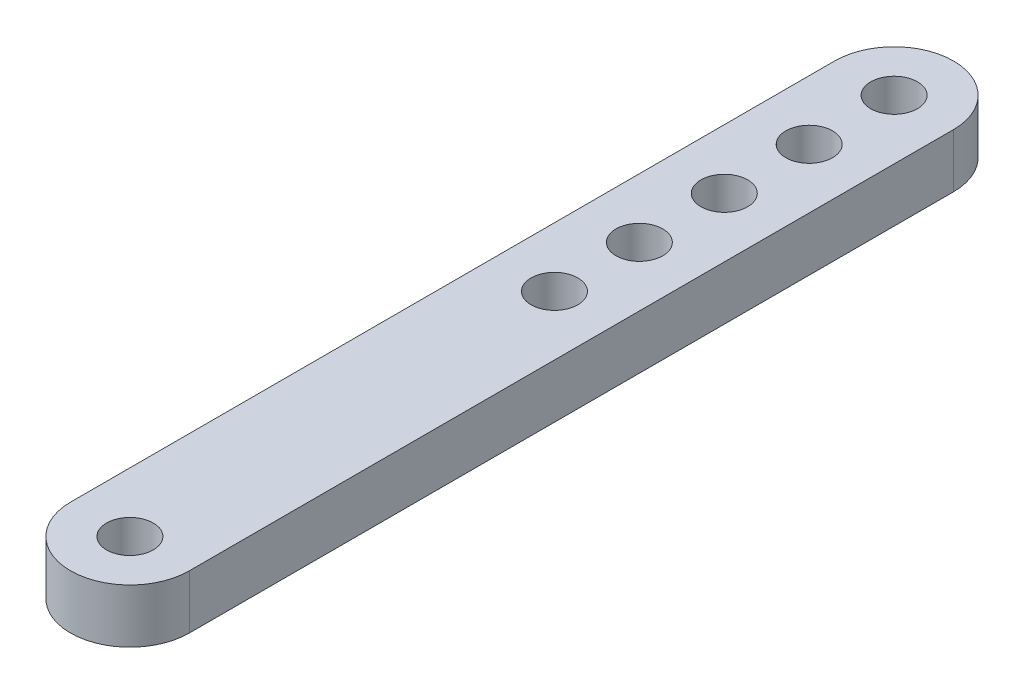
SolidWorks part; units mm, degrees
ref_plane "Front Plane" through (0, 0, 0) normal (0, 0, 1) x (1, 0, 0)
ref_plane "Top Plane" through (0, 0, 0) normal (0, 1, 0) x (1, 0, 0)
ref_plane "Right Plane" through (0, 0, 0) normal (1, 0, 0) x (0, 0, -1)
sketch "Sketch1" plane through (0, 0, 0) normal (0, 1, 0) x (1, 0, 0)
  line L0 (0, 90) -> (0, 0) construction
  line L1 (7, 90) -> (7, 0)
  line L2 (-7, 90) -> (-7, 0)
  arc A0 (7, 90) -> (-7, 90) centre (0, 90) ccw
  arc A1 (-7, 0) -> (7, 0) centre (0, 0) ccw
  circle A2 centre (0, 90) radius 2.75
  circle A3 centre (0, 0) radius 2.75
  point P2 (0, 45)
  point P11 (0, 0)
  dimension "D1" = 7
  dimension "D2" = 5.5
  dimension "D3" = 5.5
  dimension "D4" = 90
extrude "Boss-Extrude1" add sketch "Sketch1" along normal blind 6.35
sketch "Sketch2" plane through (0, 0, 0) normal (0, 1, 0) x (1, 0, 0)
  circle A0 centre (0, 90) radius 2.75
  circle A1 centre (0, 80) radius 2.75
  circle A2 centre (0, 70) radius 2.75
  circle A3 centre (0, 60) radius 2.75
  circle A4 centre (0, 50) radius 2.75
  dimension "D1" = 10
  dimension "D2" = 10
  dimension "D3" = 10
  dimension "D4" = 10
extrude "Cut-Extrude1" cut sketch "Sketch2" along normal blind 6.35
